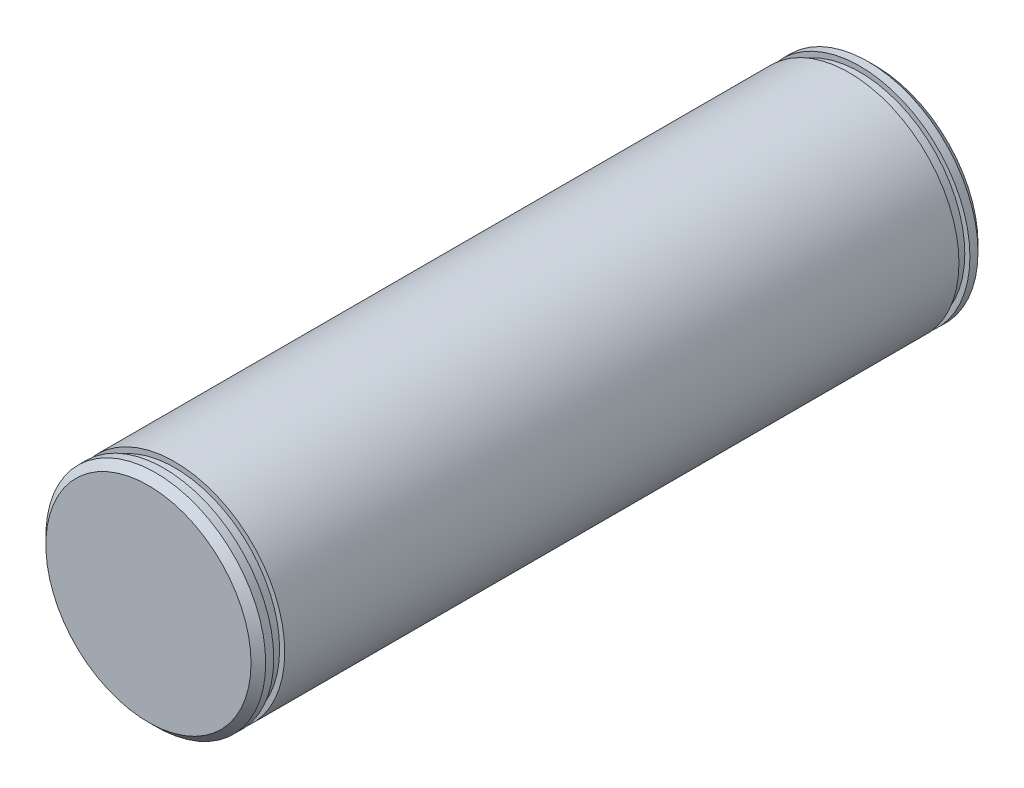
SolidWorks part; units mm, degrees
material "C45"
ref_plane "Płaszczyzna przednia" through (0, 0, 0) normal (0, 0, 1) x (1, 0, 0)
ref_plane "Płaszczyzna górna" through (0, 0, 0) normal (0, 1, 0) x (1, 0, 0)
ref_plane "Płaszczyzna prawa" through (0, 0, 0) normal (1, 0, 0) x (0, 0, -1)
ref_plane "Płaszczyzna1"
sketch "Szkic1" plane through (0, 0, 0) normal (0, 0, 1) x (1, 0, 0)
  circle A0 centre (0, 0) radius 15
  dimension "D1" = 30
extrude "Wyciągnięcie proste1" add sketch "Szkic1" along normal blind 46
sketch "Szkic2" plane through (0, 0, 46) normal (0, 0, 1) x (1, 0, 0)
  circle A0 centre (0, 0) radius 14.3
  dimension "D1" = 28.6
extrude "Wyciągnięcie proste2" add sketch "Szkic2" along normal blind 1.5
sketch "Szkic3" plane through (0, 0, 47.5) normal (0, 0, 1) x (1, 0, 0)
  circle A0 centre (0, 0) radius 15
  dimension "D1" = 30
extrude "Wyciągnięcie proste3" add sketch "Szkic3" along normal blind 2.1
chamfer "Faza1" distance 1 distance2 1 1 edges at (15, 0, 49.6)
ref_plane "Płaszczyzna2" through (0, 0, 0) normal (0, 0, -1) x (-1, 0, 0)
mirror "Odbicie lustrzane1" about plane through (0, 0, 0) normal (0, 0, -1) of bodies 103
